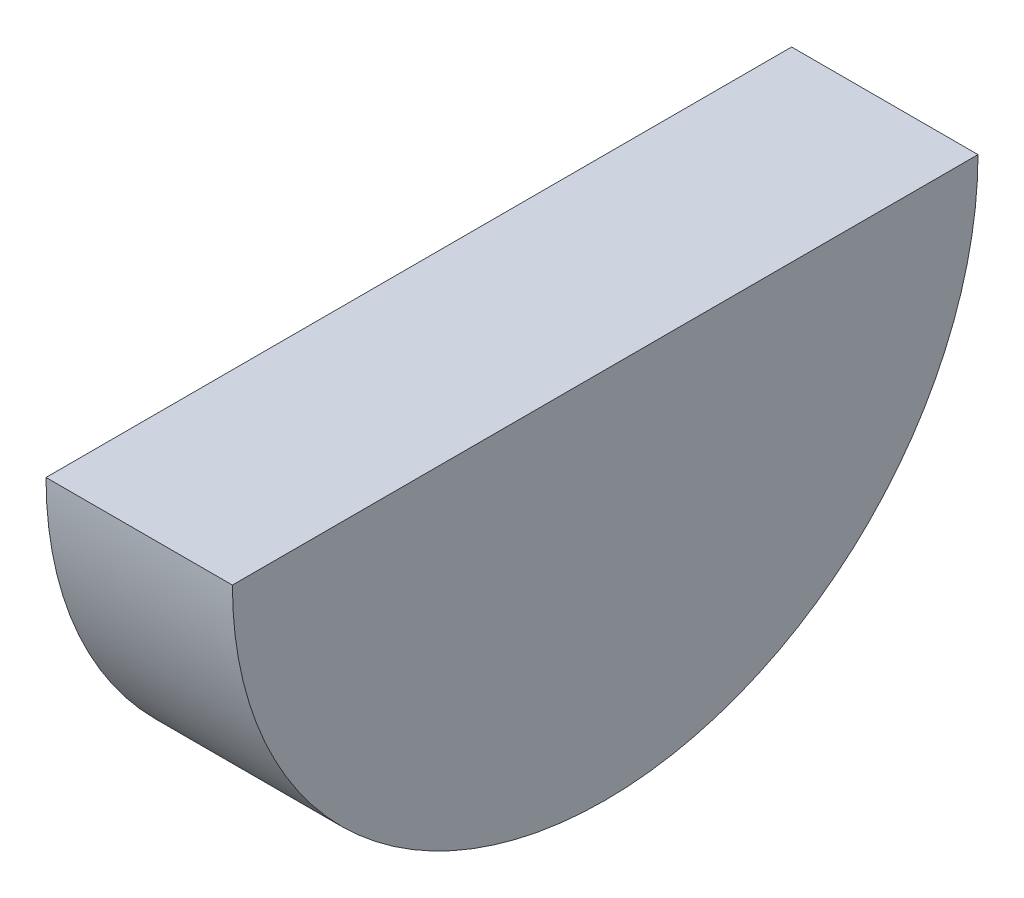
SolidWorks part; units mm, degrees
material "AISI 1020"
ref_plane "Front Plane" through (0, 0, 0) normal (0, 0, 1) x (1, 0, 0)
ref_plane "Top Plane" through (0, 0, 0) normal (0, 1, 0) x (1, 0, 0)
ref_plane "Right Plane" through (0, 0, 0) normal (1, 0, 0) x (0, 0, -1)
sketch "Sketch1" plane through (0, 0, 0) normal (1, 0, 0) x (0, 0, -1)
  line L0 (76.2, 0) -> (-76.2, 0)
  arc A0 (-76.2, 0) -> (76.2, 0) centre (0, 0) ccw
  dimension "D1" = 76.2
extrude "Boss-Extrude1" add sketch "Sketch1" along normal blind 38.1
